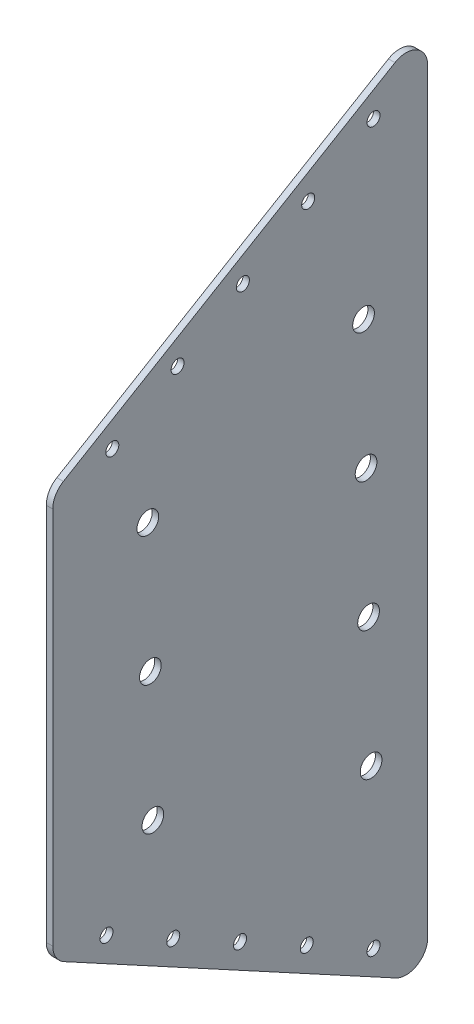
SolidWorks part; units mm, degrees
ref_plane "Front Plane" through (0, 0, 0) normal (0, 0, 1) x (1, 0, 0)
ref_plane "Top Plane" through (0, 0, 0) normal (0, 1, 0) x (1, 0, 0)
ref_plane "Right Plane" through (0, 0, 0) normal (1, 0, 0) x (0, 0, -1)
sketch "Sketch1" plane through (0, 0, 0) normal (1, 0, 0) x (0, 0, -1)
  line L0 (459.131, 411.7337) -> (459.131, 597.8495)
  line L6 (459.131, 597.8495) -> (631.9465, 700.452)
  line L7 (631.9465, 700.452) -> (631.9465, 317.9454)
  line L8 (631.9465, 317.9454) -> (459.131, 411.7337)
extrude "Boss-Extrude1" add sketch "Sketch1" along normal blind 3
sketch "Sketch3" plane through (3, 0, 0) normal (1, 0, 0) x (0, 0, -1)
  line L2 (631.9465, 700.452) -> (459.131, 597.8495) construction
  line L3 (459.131, 411.7337) -> (631.9465, 317.9454) construction
  circle A0 centre (516.6602, 620.3756) radius 3
  circle A1 centre (546.7556, 638.2436) radius 3
  circle A2 centre (576.851, 656.1116) radius 3
  circle A3 centre (514.6611, 392.9749) radius 3
  circle A4 centre (545.4229, 376.2802) radius 3
  circle A5 centre (576.1847, 359.5855) radius 3
  circle A6 centre (486.5648, 602.5076) radius 3
  circle A7 centre (606.9465, 673.9796) radius 3
  circle A8 centre (483.8993, 409.6695) radius 3
  circle A9 centre (606.9465, 342.8908) radius 3
  dimension "D4" = 6
  dimension "D5" = 6
  dimension "D6" = 6
  dimension "D12" = 6
  dimension "D13" = 6
  dimension "D14" = 6
  dimension "D17" = 6
  dimension "D18" = 6
  dimension "D19" = 6
  dimension "D20" = 6
  dimension "D3" = 10
  dimension "D7" = 35
  dimension "D8" = 35
  dimension "D9" = 10
  dimension "D10" = 10
  dimension "D11" = 10
  dimension "D15" = 35
  dimension "D16" = 35
  dimension "D21" = 10
  dimension "D22" = 10
  dimension "D23" = 35
  dimension "D24" = 35
  dimension "D25" = 10
  dimension "D26" = 10
  dimension "D27" = 10
  dimension "D28" = 10
  dimension "D29" = 35
  dimension "D30" = 35
  dimension "D31" = 25
  dimension "D32" = 25
extrude "Cut-Extrude1" cut sketch "Sketch3" against normal up to next
sketch "Sketch4" plane through (3, 0, 0) normal (1, 0, 0) x (0, 0, -1)
  circle A0 centre (602.3653, 596.2884) radius 5 construction
  circle A1 centre (603.5225, 536.2995) radius 5 construction
  circle A2 centre (604.6796, 476.3107) radius 5 construction
  circle A3 centre (605.8368, 416.3218) radius 5 construction
  circle A4 centre (502.953, 564.8567) radius 5 construction
  circle A5 centre (504.1102, 504.8679) radius 5 construction
  circle A6 centre (505.2673, 444.879) radius 5 construction
  circle A7 centre (602.3653, 596.2884) radius 5
  circle A8 centre (603.5225, 536.2995) radius 5
  circle A9 centre (604.6796, 476.3107) radius 5
  circle A10 centre (605.8368, 416.3218) radius 5
  circle A11 centre (502.953, 564.8567) radius 5
  circle A12 centre (504.1102, 504.8679) radius 5
  circle A13 centre (505.2673, 444.879) radius 5
extrude "Cut-Extrude2" cut sketch "Sketch4" against normal up to next
fillet "Fillet1" radius 10 4 edges at (1.5, 597.8495, -459.131) (1.5, 411.7337, -459.131) (1.5, 317.9454, -631.9465) (1.5, 700.452, -631.9465)
